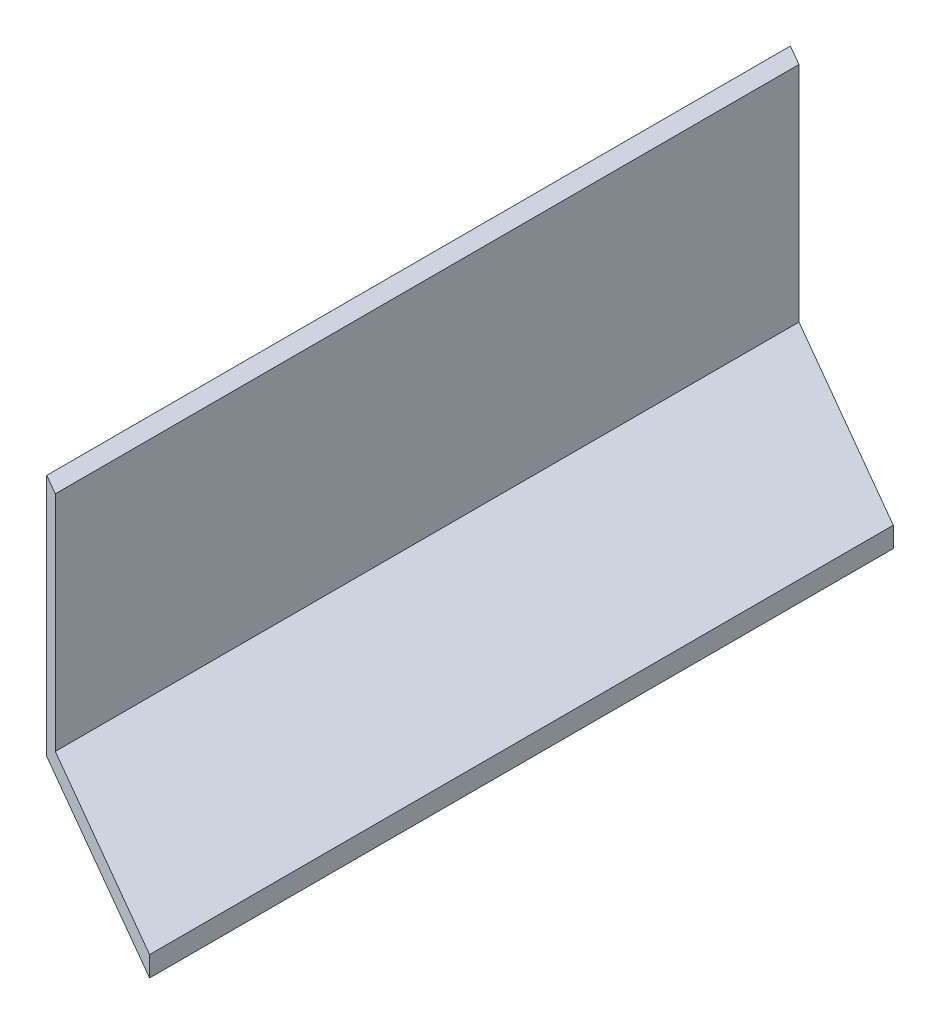
SolidWorks part; units mm, degrees
ref_plane "Front Plane" through (0, 0, 0) normal (0, 0, 1) x (1, 0, 0)
ref_plane "Top Plane" through (0, 0, 0) normal (0, 1, 0) x (1, 0, 0)
ref_plane "Right Plane" through (0, 0, 0) normal (1, 0, 0) x (0, 0, -1)
sketch "Sketch1" plane through (0, 0, 0) normal (0, 0, 1) x (1, 0, 0)
  line L1 (0, 0) -> (38.1, 0)
  line L2 (0, 0) -> (0, 38.1)
  line L3 (0, 38.1) -> (38.1, 38.1)
  line L4 (38.1, 0) -> (38.1, 38.1)
extrude "Boss-Extrude1" add sketch "Sketch1" along normal blind 138.43
sketch "Sketch2" plane through (0, 0, 138.43) normal (0, 0, 1) x (1, 0, 0)
  line L1 (38.1, 38.1) -> (3.175, 38.1)
  line L2 (38.1, 38.1) -> (38.1, 3.175)
  line L3 (38.1, 3.175) -> (3.175, 3.175)
  line L4 (3.175, 38.1) -> (3.175, 3.175)
extrude "Cut-Extrude1" cut sketch "Sketch2" against normal through all
sketch "Sketch3" plane through (0, 0, 0) normal (0, -1, 0) x (-1, 0, 0)
  line L0 (0, 0) -> (-38.1, 0)
  line L1 (-38.1, 0) -> (-38.1, -21.997)
  line L2 (-38.1, -138.43) -> (-38.1, 0) construction
  line L3 (-38.1, -21.997) -> (0, 0)
  line L4 (0, -138.43) -> (-38.1, -138.43)
  line L5 (-38.1, -138.43) -> (0, -116.433)
  line L6 (0, -138.43) -> (0, 0) construction
  line L7 (0, -116.433) -> (0, -138.43)
  dimension "D1" = 30
  dimension "D2" = 60
extrude "Cut-Extrude2" cut sketch "Sketch3" against normal blind 38.1
